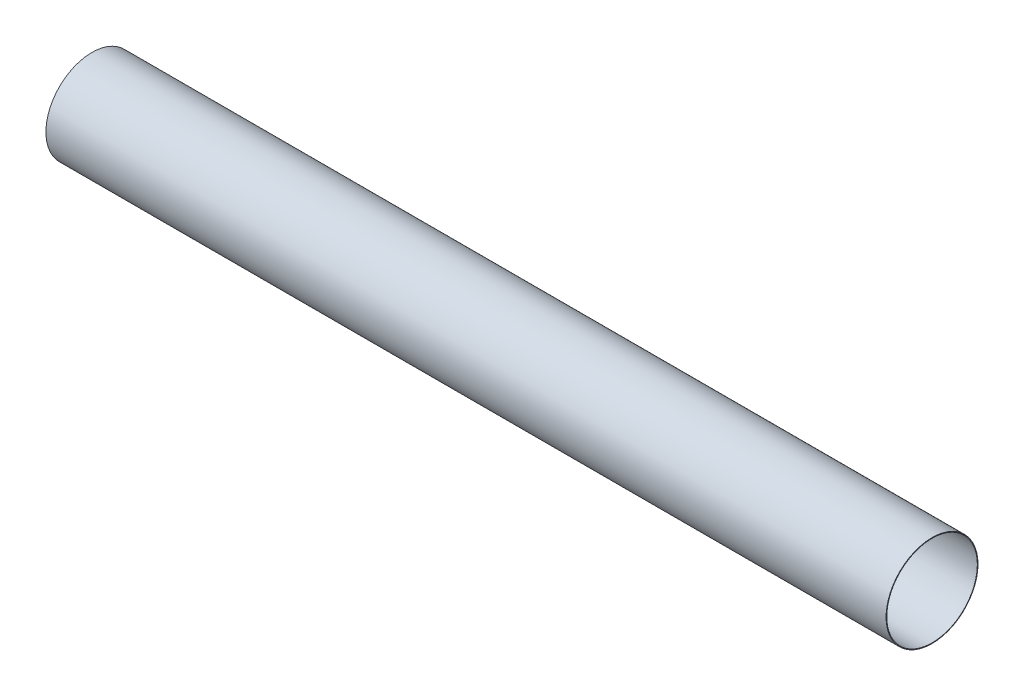
SolidWorks part; units mm, degrees
material "Thornel VCB-20 Carbon Cloth"
ref_plane "Front Plane" through (0, 0, 0) normal (0, 0, 1) x (1, 0, 0)
ref_plane "Top Plane" through (0, 0, 0) normal (0, 1, 0) x (1, 0, 0)
ref_plane "Right Plane" through (0, 0, 0) normal (1, 0, 0) x (0, 0, -1)
sketch "Skin cross section profile" plane through (0, 0, 0) normal (1, 0, 0) x (0, -1, 0)
  circle A0 centre (0, 0) radius 88.9
  circle A1 centre (0, 0) radius 87.63
  dimension "D1" = 177.8
  dimension "D2" = 1.27
extrude "Cylider skin extrude" add sketch "Skin cross section profile" along normal blind 1625.6
